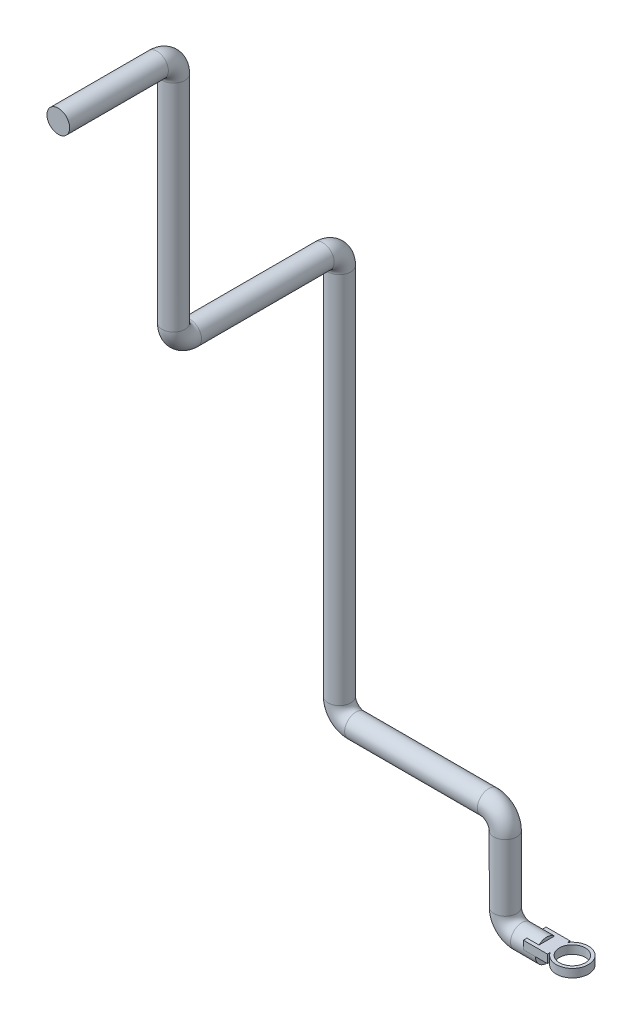
SolidWorks part; units mm, degrees
ref_plane "Alzado" through (0, 0, 0) normal (0, 0, 1) x (1, 0, 0)
ref_plane "Planta" through (0, 0, 0) normal (0, 1, 0) x (1, 0, 0)
ref_plane "Vista lateral" through (0, 0, 0) normal (1, 0, 0) x (0, 0, -1)
sketch3d "Croquis3D1"
  line L0 (0, 0, 0) -> (-30, 0, 0)
  line L1 (-50, 20, 0) -> (-50, 100, 0)
  line L2 (-70, 120, 0) -> (-230, 120, 0)
  line L3 (-250, 140, 0) -> (-250, 590.01, 0)
  line L4 (-250, 610.01, 20) -> (-250, 610.01, 180)
  line L5 (-250, 630.01, 200) -> (-250, 890.01, 200)
  line L6 (-250, 910.01, 220) -> (-250, 910.01, 339)
  arc A0 (-250, 890.01, 200) -> (-250, 910.01, 220) centre (-250, 890.01, 220) ccw
  arc A1 (-250, 610.01, 180) -> (-250, 630.01, 200) centre (-250, 630.01, 180) ccw
  arc A2 (-250, 590.01, 0) -> (-250, 610.01, 20) centre (-250, 590.01, 20) ccw
  arc A3 (-230, 120, 0) -> (-250, 140, 0) centre (-230, 140, 0) ccw
  arc A4 (-50, 100, 0) -> (-70, 120, 0) centre (-70, 100, 0) ccw
  arc A5 (-30, 0, 0) -> (-50, 20, 0) centre (-30, 20, 0) ccw
  point P12 (-250, 910.01, 200)
  point P13 (-230, 890.01, 220)
  point P16 (-250, 610.01, 200)
  point P17 (-270, 630.01, 180)
  point P20 (-250, 610.01, 0)
  point P21 (-230, 590.01, 20)
  point P24 (-250, 120, 0)
  point P25 (-230, 140, -20)
  point P28 (-50, 120, 0)
  point P29 (-70, 100, 20)
  point P32 (-50, 0, 0)
  point P33 (-30, 20, -20)
  dimension "D8" = 20
  dimension "D1" = 50
  dimension "D2" = 120
  dimension "D3" = 200
  dimension "D4" = 490.01
  dimension "D5" = 200
  dimension "D6" = 300
  dimension "D7" = 139
sketch "Croquis1" plane through (0, 0, 0) normal (1, 0, 0) x (0, 0, -1)
  circle A0 centre (0, 0) radius 13.7
  dimension "D1" = 27.4
sweep "Barrer1" add profiles "Croquis1" path "Croquis3D1"
ref_plane "Plano1" through (0, 0, 0) normal (0, 0, 1) x (1, 0, 0)
sketch "Croquis2" plane through (0, 0, 0) normal (0, 1, 0) x (1, 0, 0)
  line L0 (0, 0) -> (30.8521, 0) construction
  line L1 (-145.035, 0) -> (145.035, 0) construction
  circle A0 centre (30.8521, 0) radius 15.5693
  circle A1 centre (30.8521, 0) radius 19.3862
extrude "Saliente-Extruir1" add sketch "Croquis2" along normal blind 10 separate body
sketch "Croquis3" plane through (0, 0, 0) normal (0, 1, 0) x (1, 0, 0)
  line L1 (-14.5121, 13.7028) -> (14.5121, 13.7028)
  line L2 (-14.5121, 13.7028) -> (-14.5121, -13.7028)
  line L3 (-14.5121, -13.7028) -> (14.5121, -13.7028)
  line L4 (14.5121, 13.7028) -> (14.5121, -13.7028)
  line L5 (-14.5121, 13.7028) -> (14.5121, -13.7028) construction
  line L6 (-14.5121, -13.7028) -> (14.5121, 13.7028) construction
  point P0 (0, 0)
extrude "Saliente-Extruir2" add sketch "Croquis3" along normal blind 10
